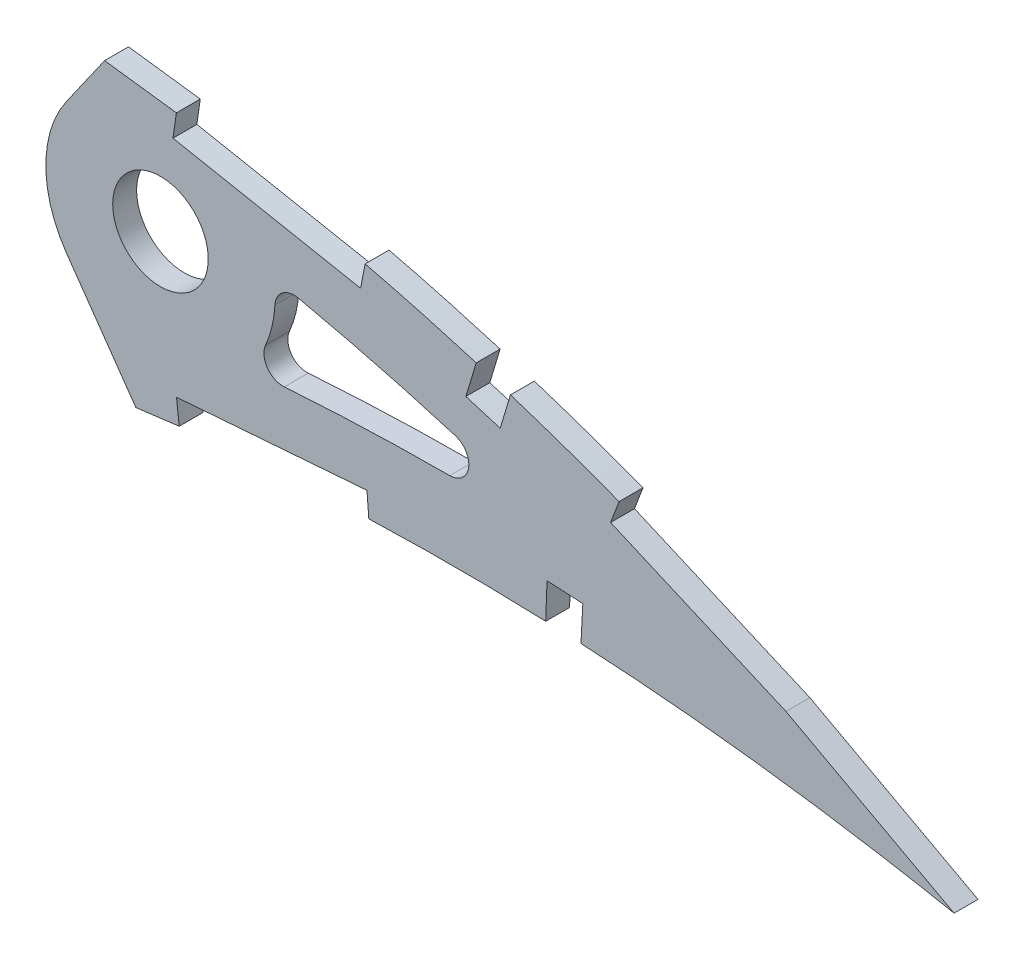
SolidWorks part; units mm, degrees
ref_plane "Front Plane" through (0, 0, 0) normal (0, 0, 1) x (1, 0, 0)
ref_plane "Top Plane" through (0, 0, 0) normal (0, 1, 0) x (1, 0, 0)
ref_plane "Right Plane" through (0, 0, 0) normal (1, 0, 0) x (0, 0, -1)
curve "Curve1"
  spline degree 3 poles (383.949, 0.5986, 0) (383.9196, 0.6168, 0) (383.802, 0.6894, 0) (383.5372, 0.8518, 0) (383.0962, 1.1224, 0) (382.4788, 1.4992, 0) (381.6856, 1.9812, 0) (380.716, 2.5651, 0) (379.5708, 3.249, 0) (378.2502, 4.0295, 0) (376.7543, 4.9032, 0) (375.0838, 5.8664, 0) (373.2387, 6.9137, 0) (371.2197, 8.0407, 0) (369.0276, 9.2423, 0) (366.6628, 10.5128, 0) (364.1261, 11.8459, 0) (361.4185, 13.2358, 0) (358.5405, 14.6749, 0) (355.4934, 16.1571, 0) (352.2782, 17.675, 0) (348.8962, 19.2207, 0) (345.3491, 20.7877, 0) (341.638, 22.3663, 0) (337.765, 23.9497, 0) (333.7318, 25.5289, 0) (329.5407, 27.0966, 0) (325.1933, 28.6428, 0) (320.6929, 30.1607, 0) (316.0417, 31.6403, 0) (311.2431, 33.0737, 0) (306.2997, 34.4516, 0) (301.2157, 35.767, 0) (295.9944, 37.0101, 0) (290.6401, 38.1728, 0) (285.1572, 39.2479, 0) (279.5502, 40.2249, 0) (273.8346, 41.1028, 0) (268.1025, 41.8331, 0) (262.3821, 42.5494, 0) (256.6703, 43.2222, 0) (250.8886, 43.8666, 0) (245.0428, 44.4788, 0) (239.1384, 45.057, 0) (233.1816, 45.5987, 0) (227.1785, 46.1022, 0) (221.135, 46.5647, 0) (215.0573, 46.9856, 0) (208.9515, 47.361, 0) (202.8242, 47.6908, 0) (196.6815, 47.9725, 0) (190.5298, 48.2044, 0) (184.3757, 48.385, 0) (178.2255, 48.5125, 0) (172.0859, 48.5861, 0) (165.9633, 48.6039, 0) (159.8643, 48.5655, 0) (153.7954, 48.4696, 0) (147.7632, 48.3149, 0) (141.7741, 48.1011, 0) (135.8345, 47.8283, 0) (129.951, 47.4942, 0) (124.1299, 47.1009, 0) (118.3778, 46.6469, 0) (112.701, 46.1319, 0) (107.1053, 45.5581, 0) (101.5971, 44.9239, 0) (96.1822, 44.2312, 0) (90.8666, 43.4813, 0) (85.6562, 42.6738, 0) (80.5566, 41.8111, 0) (75.5733, 40.894, 0) (70.7116, 39.9252, 0) (65.9768, 38.9049, 0) (61.3739, 37.8363, 0) (56.9076, 36.7211, 0) (52.5828, 35.5615, 0) (48.4038, 34.3602, 0) (44.375, 33.1199, 0) (40.5009, 31.842, 0) (36.7845, 30.5314, 0) (33.2304, 29.1889, 0) (29.8413, 27.8188, 0) (26.6212, 26.4228, 0) (23.5724, 25.0052, 0) (20.6984, 23.5677, 0) (18.0014, 22.1143, 0) (15.4839, 20.6472, 0) (13.1483, 19.1691, 0) (10.9958, 17.6837, 0) (9.0293, 16.1921, 0) (7.2493, 14.698, 0) (5.6571, 13.2036, 0) (4.255, 11.71, 0) (3.0428, 10.2198, 0) (2.0222, 8.7343, 0) (1.1933, 7.2547, 0) (0.558, 5.7822, 0) (0.1157, 4.3176, 0) (-0.1263, 2.863, 0) (-0.1866, 1.4174, 0) (-0.0621, 0.4718, 0) (0, 0, 0) knots 0 0 0 0 0.000254 0.001015 0.002283 0.004057 0.006331 0.009105 0.012374 0.016134 0.02038 0.025106 0.030306 0.035972 0.0421 0.048678 0.055702 0.06316 0.071046 0.07935 0.088063 0.097176 0.106678 0.116562 0.126814 0.137428 0.148394 0.1597 0.171338 0.183298 0.19557 0.208144 0.221012 0.234162 0.247587 0.261277 0.275223 0.289414 0.303771 0.317689 0.331784 0.34604 0.360444 0.374983 0.38964 0.404403 0.419257 0.434187 0.449177 0.464215 0.479284 0.49437 0.509458 0.524532 0.539579 0.554583 0.56953 0.584403 0.599191 0.613877 0.628447 0.642889 0.657186 0.671326 0.685294 0.699078 0.712665 0.726043 0.739198 0.752118 0.764792 0.777208 0.789356 0.801224 0.812804 0.824083 0.835055 0.84571 0.856038 0.866034 0.875689 0.884998 0.893953 0.902553 0.910789 0.918661 0.926166 0.933303 0.940071 0.946475 0.952518 0.958205 0.963547 0.968557 0.97325 0.977651 0.981787 0.985694 0.989415 0.993001 0.996508 1 1 1 1
curve "Curve2"
  spline degree 3 poles (0, 0, 0) (0.0986, -0.4654, 0) (0.2962, -1.3985, 0) (0.8332, -2.7416, 0) (1.5434, -4.0328, 0) (2.4415, -5.2686, 0) (3.5218, -6.4485, 0) (4.7818, -7.574, 0) (6.2202, -8.6443, 0) (7.8352, -9.659, 0) (9.6244, -10.6191, 0) (11.5859, -11.5241, 0) (13.7178, -12.3737, 0) (16.0178, -13.1667, 0) (18.4831, -13.9043, 0) (21.1113, -14.5848, 0) (23.8995, -15.2091, 0) (26.845, -15.7756, 0) (29.9446, -16.2848, 0) (33.195, -16.7366, 0) (36.593, -17.1311, 0) (40.1351, -17.4676, 0) (43.8179, -17.7467, 0) (47.6377, -17.9687, 0) (51.5909, -18.1343, 0) (55.6735, -18.2428, 0) (59.8817, -18.2959, 0) (64.2115, -18.2945, 0) (68.6589, -18.238, 0) (73.2199, -18.1297, 0) (77.8902, -17.9689, 0) (82.6657, -17.7575, 0) (87.5419, -17.4976, 0) (92.5144, -17.1902, 0) (97.5791, -16.8365, 0) (102.7313, -16.4394, 0) (107.9665, -16, 0) (113.2801, -15.5207, 0) (118.6674, -15.0039, 0) (124.1237, -14.4514, 0) (129.6442, -13.8657, 0) (135.2241, -13.2487, 0) (140.8584, -12.6036, 0) (146.5422, -11.9317, 0) (152.2705, -11.2369, 0) (158.0381, -10.5203, 0) (163.84, -9.7848, 0) (169.6711, -9.0339, 0) (175.5259, -8.2674, 0) (181.3995, -7.4908, 0) (187.2862, -6.7036, 0) (193.1809, -5.9096, 0) (199.0781, -5.1115, 0) (204.9721, -4.3094, 0) (210.8578, -3.5066, 0) (216.7295, -2.7054, 0) (222.5817, -1.9059, 0) (228.409, -1.112, 0) (234.2055, -0.3236, 0) (239.9659, 0.4577, 0) (245.6847, 1.2295, 0) (251.3565, 1.9909, 0) (256.9754, 2.7413, 0) (262.5357, 3.4812, 0) (267.9487, 4.188, 0) (273.2002, 4.8993, 0) (278.3079, 5.4825, 0) (283.3519, 5.9802, 0) (288.3377, 6.3883, 0) (293.259, 6.7125, 0) (298.1104, 6.9553, 0) (302.886, 7.1201, 0) (307.5799, 7.2116, 0) (312.186, 7.2323, 0) (316.6983, 7.1886, 0) (321.1107, 7.0842, 0) (325.4171, 6.9238, 0) (329.6115, 6.7126, 0) (333.688, 6.4566, 0) (337.6405, 6.1594, 0) (341.4634, 5.828, 0) (345.1508, 5.4673, 0) (348.6971, 5.0813, 0) (352.0971, 4.6782, 0) (355.3453, 4.2606, 0) (358.4369, 3.8354, 0) (361.3669, 3.4069, 0) (364.1307, 2.9806, 0) (366.7239, 2.5605, 0) (369.1422, 2.1521, 0) (371.3821, 1.7594, 0) (373.4394, 1.3862, 0) (375.3115, 1.0371, 0) (376.9946, 0.7139, 0) (378.4864, 0.4219, 0) (379.7842, 0.1625, 0) (380.886, -0.0608, 0) (381.79, -0.247, 0) (382.4947, -0.3932, 0) (382.9989, -0.4995, 0) (383.3019, -0.5627, 0) (383.4365, -0.5914, 0) (383.4701, -0.5986, 0) knots 0 0 0 0 0.003638 0.007293 0.011028 0.014901 0.018963 0.023258 0.027821 0.032679 0.037853 0.043362 0.049215 0.055422 0.061989 0.068918 0.076211 0.083868 0.091887 0.100266 0.109 0.118085 0.127515 0.137285 0.147388 0.157816 0.168563 0.179619 0.190977 0.202627 0.21456 0.226767 0.239236 0.251959 0.264924 0.27812 0.291536 0.30516 0.318981 0.332985 0.347163 0.361499 0.375981 0.390597 0.405333 0.420175 0.43511 0.450124 0.465203 0.480333 0.495501 0.51069 0.525887 0.541078 0.556247 0.571382 0.586466 0.601485 0.616424 0.631269 0.646007 0.660621 0.675098 0.689423 0.703582 0.716908 0.730009 0.742952 0.755726 0.76832 0.780724 0.792927 0.804916 0.816679 0.828204 0.839475 0.850481 0.861208 0.871639 0.881763 0.891564 0.901027 0.910139 0.918884 0.927249 0.935221 0.942785 0.949928 0.956638 0.962904 0.968712 0.974054 0.978918 0.983297 0.98718 0.990561 0.993433 0.995791 0.99763 0.998946 0.999737 1 1 1 1
sketch "Sketch1" plane through (0, 0, 0) normal (0, 0, 1) x (1, 0, 0)
  line L23 (383.4597, -0.5986) -> (387.1511, -1.386)
  line L24 (383.9386, 0.5986) -> (387.1511, -1.386)
  spline S4 degree 3 poles (0, 0) (0.0986, -0.4654) (0.2962, -1.3984) (0.8332, -2.7416) (1.5433, -4.0327) (2.4415, -5.2684) (3.5217, -6.4484) (4.7816, -7.5738) (6.22, -8.6441) (7.835, -9.6587) (9.6242, -10.6188) (11.5856, -11.5238) (13.7174, -12.3733) (16.0173, -13.1663) (18.4826, -13.9039) (21.1108, -14.5844) (23.8989, -15.2087) (26.8443, -15.7751) (29.9438, -16.2844) (33.1941, -16.7361) (36.592, -17.1306) (40.134, -17.4671) (43.8167, -17.7462) (47.6365, -17.9682) (51.5895, -18.1338) (55.672, -18.2423) (59.88, -18.2954) (64.2098, -18.294) (68.657, -18.2375) (73.2179, -18.1293) (77.8881, -17.9684) (82.6634, -17.757) (87.5395, -17.4972) (92.5119, -17.1897) (97.5764, -16.836) (102.7286, -16.439) (107.9636, -15.9995) (113.2771, -15.5202) (118.6642, -15.0035) (124.1204, -14.451) (129.6407, -13.8653) (135.2204, -13.2483) (140.8546, -12.6033) (146.5382, -11.9314) (152.2664, -11.2365) (158.0338, -10.52) (163.8356, -9.7845) (169.6665, -9.0336) (175.5212, -8.2672) (181.3946, -7.4906) (187.2811, -6.7034) (193.1757, -5.9095) (199.0727, -5.1113) (204.9666, -4.3092) (210.8521, -3.5065) (216.7237, -2.7054) (222.5757, -1.9059) (228.4028, -1.112) (234.1992, -0.3236) (239.9594, 0.4576) (245.6781, 1.2294) (251.3497, 1.9908) (256.9684, 2.7413) (262.5286, 3.4811) (267.9415, 4.1879) (273.1928, 4.8992) (278.3003, 5.4823) (283.3443, 5.98) (288.3299, 6.3881) (293.2511, 6.7123) (298.1023, 6.9552) (302.8778, 7.1199) (307.5715, 7.2114) (312.1776, 7.2321) (316.6897, 7.1884) (321.102, 7.084) (325.4083, 6.9236) (329.6026, 6.7124) (333.679, 6.4564) (337.6313, 6.1592) (341.4541, 5.8278) (345.1414, 5.4671) (348.6876, 5.0812) (352.0875, 4.6781) (355.3357, 4.2605) (358.4272, 3.8353) (361.3571, 3.4068) (364.1208, 2.9805) (366.7139, 2.5604) (369.1322, 2.1521) (371.372, 1.7594) (373.4293, 1.3862) (375.3013, 1.0371) (376.9844, 0.7139) (378.4761, 0.4219) (379.7739, 0.1625) (380.8757, -0.0608) (381.7796, -0.247) (382.4844, -0.3932) (382.9885, -0.4994) (383.2915, -0.5627) (383.4261, -0.5914) (383.4597, -0.5986) knots 0 0 0 0 0.003638 0.007293 0.011028 0.014901 0.018963 0.023258 0.027821 0.032679 0.037853 0.043362 0.049215 0.055422 0.061989 0.068918 0.076211 0.083868 0.091887 0.100266 0.109 0.118085 0.127515 0.137285 0.147388 0.157816 0.168563 0.179619 0.190977 0.202627 0.21456 0.226767 0.239236 0.251959 0.264924 0.27812 0.291536 0.30516 0.318981 0.332985 0.347163 0.361499 0.375981 0.390597 0.405333 0.420175 0.43511 0.450124 0.465203 0.480333 0.495501 0.51069 0.525887 0.541078 0.556247 0.571382 0.586466 0.601485 0.616424 0.631269 0.646007 0.660621 0.675098 0.689423 0.703582 0.716908 0.730009 0.742952 0.755726 0.76832 0.780724 0.792927 0.804916 0.816679 0.828204 0.839475 0.850481 0.861208 0.871639 0.881763 0.891564 0.901027 0.910139 0.918884 0.927249 0.935221 0.942785 0.949928 0.956638 0.962904 0.968712 0.974054 0.978918 0.983297 0.98718 0.990561 0.993433 0.995791 0.99763 0.998946 0.999737 1 1 1 1
  spline S5 degree 3 poles (383.9386, 0.5986) (383.9092, 0.6167) (383.7916, 0.6893) (383.5268, 0.8518) (383.0858, 1.1223) (382.4685, 1.4991) (381.6752, 1.9811) (380.7057, 2.565) (379.5606, 3.2489) (378.24, 4.0294) (376.7441, 4.9031) (375.0736, 5.8662) (373.2286, 6.9135) (371.2097, 8.0405) (369.0176, 9.242) (366.6529, 10.5125) (364.1162, 11.8456) (361.4087, 13.2354) (358.5307, 14.6745) (355.4837, 16.1566) (352.2687, 17.6745) (348.8867, 19.2201) (345.3398, 20.7871) (341.6288, 22.3657) (337.7559, 23.949) (333.7228, 25.5282) (329.5317, 27.0959) (325.1845, 28.642) (320.6843, 30.1598) (316.0332, 31.6395) (311.2346, 33.0728) (306.2914, 34.4507) (301.2076, 35.766) (295.9864, 37.0091) (290.6322, 38.1717) (285.1495, 39.2469) (279.5426, 40.2238) (273.8272, 41.1017) (268.0952, 41.832) (262.375, 42.5482) (256.6633, 43.2211) (250.8818, 43.8654) (245.0361, 44.4776) (239.1319, 45.0558) (233.1753, 45.5974) (227.1724, 46.1009) (221.129, 46.5635) (215.0515, 46.9843) (208.9459, 47.3597) (202.8187, 47.6895) (196.6762, 47.9712) (190.5246, 48.2031) (184.3707, 48.3836) (178.2206, 48.5111) (172.0812, 48.5848) (165.9588, 48.6026) (159.86, 48.5642) (153.7912, 48.4683) (147.7592, 48.3136) (141.7702, 48.0998) (135.8308, 47.827) (129.9475, 47.4929) (124.1266, 47.0997) (118.3746, 46.6456) (112.6979, 46.1306) (107.1024, 45.5568) (101.5944, 44.9227) (96.1796, 44.23) (90.8641, 43.4801) (85.6539, 42.6727) (80.5544, 41.81) (75.5713, 40.8929) (70.7097, 39.9241) (65.975, 38.9039) (61.3722, 37.8353) (56.906, 36.7201) (52.5814, 35.5606) (48.4025, 34.3593) (44.3738, 33.119) (40.4998, 31.8412) (36.7835, 30.5306) (33.2295, 29.1881) (29.8405, 27.818) (26.6204, 26.4221) (23.5718, 25.0045) (20.6979, 23.5671) (18.0009, 22.1137) (15.4834, 20.6466) (13.148, 19.1685) (10.9955, 17.6833) (9.029, 16.1917) (7.2491, 14.6976) (5.657, 13.2033) (4.2548, 11.7097) (3.0427, 10.2196) (2.0221, 8.734) (1.1932, 7.2545) (0.558, 5.782) (0.1157, 4.3174) (-0.1263, 2.8629) (-0.1866, 1.4173) (-0.0621, 0.4717) (0, 0) knots 0 0 0 0 0.000254 0.001015 0.002283 0.004057 0.006331 0.009105 0.012374 0.016134 0.02038 0.025106 0.030306 0.035972 0.0421 0.048678 0.055702 0.06316 0.071046 0.07935 0.088063 0.097176 0.106678 0.116562 0.126814 0.137428 0.148394 0.1597 0.171338 0.183298 0.19557 0.208144 0.221012 0.234162 0.247587 0.261277 0.275223 0.289414 0.303771 0.317689 0.331784 0.34604 0.360444 0.374983 0.38964 0.404403 0.419257 0.434187 0.449177 0.464215 0.479284 0.49437 0.509458 0.524532 0.539579 0.554583 0.56953 0.584403 0.599191 0.613877 0.628447 0.642889 0.657186 0.671326 0.685294 0.699078 0.712665 0.726043 0.739198 0.752118 0.764792 0.777208 0.789356 0.801224 0.812804 0.824083 0.835055 0.84571 0.856038 0.866034 0.875689 0.884998 0.893953 0.902553 0.910789 0.918661 0.926166 0.933303 0.940071 0.946475 0.952518 0.958205 0.963547 0.968557 0.97325 0.977651 0.981787 0.985694 0.989415 0.993001 0.996508 1 1 1 1
extrude "Boss-Extrude1" add sketch "Sketch1" along normal blind 3.175
sketch "Sketch3" plane through (0, 0, 0) normal (0, 0, -1) x (-1, 0, 0)
  circle A1 centre (-272.4199, 26.2554) radius 6.35
extrude "Cut-Extrude2" cut sketch "Sketch3" against normal blind 7.62
sketch "Sketch4" plane through (0, 0, 3.175) normal (0, 0, 1) x (1, 0, 0)
  line L0 (272.4199, 26.2554) -> (275.6183, 26.2554)
  line L1 (259.936, 34.9967) -> (264.9932, 42.2191)
  line L2 (259.936, 17.5141) -> (269.1511, 4.3535)
  circle A0 centre (272.4199, 26.2554) radius 6.35 construction
  circle A1 centre (272.4199, 26.2554) radius 6.35
  circle A2 centre (272.4199, 26.2554) radius 15.24
  spline S0 degree 3 poles (-2900.5811, -762.1564) (60.7171, 58.1372) (-7.1311, 17.1797) (0.8332, -2.7416) (1.5433, -4.0327) (2.4415, -5.2684) (3.5217, -6.4484) (4.7816, -7.5738) (6.22, -8.6441) (7.835, -9.6587) (9.6242, -10.6188) (11.5856, -11.5238) (13.7174, -12.3733) (16.0173, -13.1663) (18.4826, -13.9039) (21.1108, -14.5844) (23.8989, -15.2087) (26.8443, -15.7751) (29.9438, -16.2844) (33.1941, -16.7361) (36.592, -17.1306) (40.134, -17.4671) (43.8167, -17.7462) (47.6365, -17.9682) (51.5895, -18.1338) (55.672, -18.2423) (59.88, -18.2954) (64.2098, -18.294) (68.657, -18.2375) (73.2179, -18.1293) (77.8881, -17.9684) (82.6634, -17.757) (87.5395, -17.4972) (92.5119, -17.1897) (97.5764, -16.836) (102.7286, -16.439) (107.9636, -15.9995) (113.2771, -15.5202) (118.6642, -15.0035) (124.1204, -14.451) (129.6407, -13.8653) (135.2204, -13.2483) (140.8546, -12.6033) (146.5382, -11.9314) (152.2664, -11.2365) (158.0338, -10.52) (163.8356, -9.7845) (169.6665, -9.0336) (175.5212, -8.2672) (181.3946, -7.4906) (187.2811, -6.7034) (193.1757, -5.9095) (199.0727, -5.1113) (204.9666, -4.3092) (210.8521, -3.5065) (216.7237, -2.7054) (222.5757, -1.9059) (228.4028, -1.112) (234.1992, -0.3236) (239.9594, 0.4576) (245.6781, 1.2294) (251.3497, 1.9908) (256.9684, 2.7413) (262.5286, 3.4811) (267.9415, 4.1879) (273.1928, 4.8992) (278.3003, 5.4823) (283.3443, 5.98) (288.3299, 6.3881) (293.2511, 6.7123) (298.1023, 6.9552) (302.8778, 7.1199) (307.5715, 7.2114) (312.1776, 7.2321) (316.6897, 7.1884) (321.102, 7.084) (325.4083, 6.9236) (329.6026, 6.7124) (333.679, 6.4564) (337.6313, 6.1592) (341.4541, 5.8278) (345.1414, 5.4671) (348.6876, 5.0812) (352.0875, 4.6781) (355.3357, 4.2605) (358.4272, 3.8353) (361.3571, 3.4068) (364.1208, 2.9805) (366.7139, 2.5604) (369.1322, 2.1521) (371.372, 1.7594) (373.4293, 1.3862) (375.3013, 1.0371) (376.9844, 0.7139) (378.4761, 0.4219) (379.7739, 0.1625) (380.8757, -0.0608) (381.7796, -0.247) (382.4844, -0.3932) (382.9885, -0.4994) (397.7614, -3.5828) (410.8952, -13.5854) (1047.3532, 2924.2375) knots -0.152541 -0.152541 -0.152541 -0.152541 0.003638 0.007293 0.011028 0.014901 0.018963 0.023258 0.027821 0.032679 0.037853 0.043362 0.049215 0.055422 0.061989 0.068918 0.076211 0.083868 0.091887 0.100266 0.109 0.118085 0.127515 0.137285 0.147388 0.157816 0.168563 0.179619 0.190977 0.202627 0.21456 0.226767 0.239236 0.251959 0.264924 0.27812 0.291536 0.30516 0.318981 0.332985 0.347163 0.361499 0.375981 0.390597 0.405333 0.420175 0.43511 0.450124 0.465203 0.480333 0.495501 0.51069 0.525887 0.541078 0.556247 0.571382 0.586466 0.601485 0.616424 0.631269 0.646007 0.660621 0.675098 0.689423 0.703582 0.716908 0.730009 0.742952 0.755726 0.76832 0.780724 0.792927 0.804916 0.816679 0.828204 0.839475 0.850481 0.861208 0.871639 0.881763 0.891564 0.901027 0.910139 0.918884 0.927249 0.935221 0.942785 0.949928 0.956638 0.962904 0.968712 0.974054 0.978918 0.983297 0.98718 0.990561 0.993433 0.995791 0.99763 0.998946 0.999737 1.113214 1.113214 1.113214 1.113214 only from (0, 0) to (383.4597, -0.5986) construction
  spline S1 degree 3 poles (1998.8466, 2527.3991) (408.7537, -22.1004) (397.8856, -7.9557) (383.5268, 0.8518) (383.0858, 1.1223) (382.4685, 1.4991) (381.6752, 1.9811) (380.7057, 2.565) (379.5606, 3.2489) (378.24, 4.0294) (376.7441, 4.9031) (375.0736, 5.8662) (373.2286, 6.9135) (371.2097, 8.0405) (369.0176, 9.242) (366.6529, 10.5125) (364.1162, 11.8456) (361.4087, 13.2354) (358.5307, 14.6745) (355.4837, 16.1566) (352.2687, 17.6745) (348.8867, 19.2201) (345.3398, 20.7871) (341.6288, 22.3657) (337.7559, 23.949) (333.7228, 25.5282) (329.5317, 27.0959) (325.1845, 28.642) (320.6843, 30.1598) (316.0332, 31.6395) (311.2346, 33.0728) (306.2914, 34.4507) (301.2076, 35.766) (295.9864, 37.0091) (290.6322, 38.1717) (285.1495, 39.2469) (279.5426, 40.2238) (273.8272, 41.1017) (268.0952, 41.832) (262.375, 42.5482) (256.6633, 43.2211) (250.8818, 43.8654) (245.0361, 44.4776) (239.1319, 45.0558) (233.1753, 45.5974) (227.1724, 46.1009) (221.129, 46.5635) (215.0515, 46.9843) (208.9459, 47.3597) (202.8187, 47.6895) (196.6762, 47.9712) (190.5246, 48.2031) (184.3707, 48.3836) (178.2206, 48.5111) (172.0812, 48.5848) (165.9588, 48.6026) (159.86, 48.5642) (153.7912, 48.4683) (147.7592, 48.3136) (141.7702, 48.0998) (135.8308, 47.827) (129.9475, 47.4929) (124.1266, 47.0997) (118.3746, 46.6456) (112.6979, 46.1306) (107.1024, 45.5568) (101.5944, 44.9227) (96.1796, 44.23) (90.8641, 43.4801) (85.6539, 42.6727) (80.5544, 41.81) (75.5713, 40.8929) (70.7097, 39.9241) (65.975, 38.9039) (61.3722, 37.8353) (56.906, 36.7201) (52.5814, 35.5606) (48.4025, 34.3593) (44.3738, 33.119) (40.4998, 31.8412) (36.7835, 30.5306) (33.2295, 29.1881) (29.8405, 27.818) (26.6204, 26.4221) (23.5718, 25.0045) (20.6979, 23.5671) (18.0009, 22.1137) (15.4834, 20.6466) (13.148, 19.1685) (10.9955, 17.6833) (9.029, 16.1917) (7.2491, 14.6976) (5.657, 13.2033) (4.2548, 11.7097) (3.0427, 10.2196) (2.0221, 8.734) (1.1932, 7.2545) (0.558, 5.782) (0.1157, 4.3174) (-0.1263, 2.8629) (-1.0184, -18.5368) (76.7539, -34.5403) (-2989.0976, -246.1964) knots -0.121519 -0.121519 -0.121519 -0.121519 0.000254 0.001015 0.002283 0.004057 0.006331 0.009105 0.012374 0.016134 0.02038 0.025106 0.030306 0.035972 0.0421 0.048678 0.055702 0.06316 0.071046 0.07935 0.088063 0.097176 0.106678 0.116562 0.126814 0.137428 0.148394 0.1597 0.171338 0.183298 0.19557 0.208144 0.221012 0.234162 0.247587 0.261277 0.275223 0.289414 0.303771 0.317689 0.331784 0.34604 0.360444 0.374983 0.38964 0.404403 0.419257 0.434187 0.449177 0.464215 0.479284 0.49437 0.509458 0.524532 0.539579 0.554583 0.56953 0.584403 0.599191 0.613877 0.628447 0.642889 0.657186 0.671326 0.685294 0.699078 0.712665 0.726043 0.739198 0.752118 0.764792 0.777208 0.789356 0.801224 0.812804 0.824083 0.835055 0.84571 0.856038 0.866034 0.875689 0.884998 0.893953 0.902553 0.910789 0.918661 0.926166 0.933303 0.940071 0.946475 0.952518 0.958205 0.963547 0.968557 0.97325 0.977651 0.981787 0.985694 0.989415 0.993001 0.996508 1.146107 1.146107 1.146107 1.146107 only from (383.9386, 0.5986) to (0, 0) construction
  spline S2 degree 3 poles (161.4571, -10.0855) (162.2464, -9.9853) (164.9804, -9.6371) (169.6665, -9.0336) (175.5212, -8.2672) (181.3946, -7.4906) (187.2811, -6.7034) (193.1757, -5.9095) (199.0727, -5.1113) (204.9666, -4.3092) (210.8521, -3.5065) (216.7237, -2.7054) (222.5757, -1.9059) (228.4028, -1.112) (234.1992, -0.3236) (239.9594, 0.4576) (245.6781, 1.2294) (251.3497, 1.9908) (256.9684, 2.7413) (262.5286, 3.4811) (267.9415, 4.1879) (273.1928, 4.8992) (278.3003, 5.4823) (283.3443, 5.98) (288.3299, 6.3881) (293.2511, 6.7123) (298.1023, 6.9552) (302.8778, 7.1199) (307.5715, 7.2114) (312.1776, 7.2321) (316.6897, 7.1884) (321.102, 7.084) (325.4083, 6.9236) (329.6026, 6.7124) (333.679, 6.4564) (337.6313, 6.1592) (341.4541, 5.8278) (345.1414, 5.4671) (348.6876, 5.0812) (352.0875, 4.6781) (355.3357, 4.2605) (358.4272, 3.8353) (361.3571, 3.4068) (364.1208, 2.9805) (366.7139, 2.5604) (369.1322, 2.1521) (371.372, 1.7594) (373.4293, 1.3862) (375.3013, 1.0371) (376.9844, 0.7139) (378.4761, 0.4219) (379.7739, 0.1625) (380.8757, -0.0608) (381.7796, -0.247) (382.4844, -0.3932) (382.9885, -0.4994) (383.2915, -0.5627) (383.4261, -0.5914) (383.4597, -0.5986) knots 0.429016 0.429016 0.429016 0.429016 0.43511 0.450124 0.465203 0.480333 0.495501 0.51069 0.525887 0.541078 0.556247 0.571382 0.586466 0.601485 0.616424 0.631269 0.646007 0.660621 0.675098 0.689423 0.703582 0.716908 0.730009 0.742952 0.755726 0.76832 0.780724 0.792927 0.804916 0.816679 0.828204 0.839475 0.850481 0.861208 0.871639 0.881763 0.891564 0.901027 0.910139 0.918884 0.927249 0.935221 0.942785 0.949928 0.956638 0.962904 0.968712 0.974054 0.978918 0.983297 0.98718 0.990561 0.993433 0.995791 0.99763 0.998946 0.999737 1 1 1 1
  spline S3 degree 3 poles (383.9386, 0.5986) (383.9092, 0.6167) (383.7916, 0.6893) (383.5268, 0.8518) (383.0858, 1.1223) (382.4685, 1.4991) (381.6752, 1.9811) (380.7057, 2.565) (379.5606, 3.2489) (378.24, 4.0294) (376.7441, 4.9031) (375.0736, 5.8662) (373.2286, 6.9135) (371.2097, 8.0405) (369.0176, 9.242) (366.6529, 10.5125) (364.1162, 11.8456) (361.4087, 13.2354) (358.5307, 14.6745) (355.4837, 16.1566) (352.2687, 17.6745) (348.8867, 19.2201) (345.3398, 20.7871) (341.6288, 22.3657) (337.7559, 23.949) (333.7228, 25.5282) (329.5317, 27.0959) (325.1845, 28.642) (320.6843, 30.1598) (316.0332, 31.6395) (311.2346, 33.0728) (306.2914, 34.4507) (301.2076, 35.766) (295.9864, 37.0091) (290.6322, 38.1717) (285.1495, 39.2469) (279.5426, 40.2238) (273.8272, 41.1017) (268.0952, 41.832) (262.375, 42.5482) (256.6633, 43.2211) (250.8818, 43.8654) (245.0361, 44.4776) (239.1319, 45.0558) (233.1753, 45.5974) (227.1724, 46.1009) (221.129, 46.5635) (215.0515, 46.9843) (208.9459, 47.3597) (202.8187, 47.6895) (196.6762, 47.9712) (190.5246, 48.2031) (184.3707, 48.3836) (178.2206, 48.5111) (172.0812, 48.5848) (165.9588, 48.6026) (159.86, 48.5642) (153.5038, 48.4638) (149.182, 48.3499) (146.8838, 48.276) knots 0 0 0 0 0.000254 0.001015 0.002283 0.004057 0.006331 0.009105 0.012374 0.016134 0.02038 0.025106 0.030306 0.035972 0.0421 0.048678 0.055702 0.06316 0.071046 0.07935 0.088063 0.097176 0.106678 0.116562 0.126814 0.137428 0.148394 0.1597 0.171338 0.183298 0.19557 0.208144 0.221012 0.234162 0.247587 0.261277 0.275223 0.289414 0.303771 0.317689 0.331784 0.34604 0.360444 0.374983 0.38964 0.404403 0.419257 0.434187 0.449177 0.464215 0.479284 0.49437 0.509458 0.524532 0.539579 0.554583 0.56953 0.584403 0.601304 0.601304 0.601304 0.601304
  spline S4 degree 1 poles (378.5989, -8.0451) (147.21, 38.1213) knots 0 0 1 1 construction
  spline S5 degree 3 poles (378.5989, -8.0451) (378.472, -7.9667) (378.2234, -7.8142) (377.6805, -7.4812) (376.7611, -6.9205) (374.9109, -5.8032) (371.1788, -3.5966) (363.6516, 0.6712) (348.2892, 8.639) (330.0962, 16.359) (311.3792, 22.5636) (297.107, 26.4342) (285.0856, 28.9814) (276.5539, 30.4164) (271.7323, 31.12) (268.0333, 31.5987) (264.2273, 32.0776) (259.2208, 32.6948) (250.4292, 33.7129) (237.8617, 35.009) (222.7587, 36.2937) (202.6061, 37.6338) (177.3909, 38.5745) (157.2697, 38.4445) (147.21, 38.1213) knots 0 0 0 0 0.001174 0.002349 0.004698 0.009395 0.018791 0.037581 0.075163 0.150326 0.187907 0.225489 0.26307 0.281861 0.291256 0.300652 0.310047 0.319443 0.338233 0.375815 0.413396 0.450978 0.526141 0.601304 0.601304 0.601304 0.601304
  spline S6 degree 1 poles (160.178, -0.0063) (385.5793, 9.3379) knots 0 0 1 1 construction
  spline S7 degree 3 poles (160.178, -0.0063) (169.3975, 1.1637) (187.8091, 3.6001) (210.885, 6.7523) (229.3545, 9.2731) (243.2292, 11.1537) (254.7583, 12.7013) (262.905, 13.7751) (267.4672, 14.3775) (270.981, 14.8497) (274.6098, 15.2908) (279.3773, 15.8089) (285.3756, 16.3645) (292.5728, 16.8641) (302.1885, 17.3159) (314.2133, 17.4755) (333.4344, 16.8874) (352.5648, 15.0706) (369.1185, 12.5101) (377.3698, 10.9967) (381.4564, 10.1902) (383.3728, 9.7984) (384.2388, 9.6192) (384.6955, 9.524) (385.0455, 9.4502) (385.329, 9.391) (385.4982, 9.3552) (385.5793, 9.3379) knots 0.429016 0.429016 0.429016 0.429016 0.500389 0.571762 0.607448 0.643135 0.678821 0.696665 0.705586 0.714508 0.723429 0.732351 0.750194 0.768038 0.785881 0.821567 0.857254 0.928627 0.964313 0.982157 0.991078 0.995539 0.996654 0.99777 0.998885 0.999442 1 1 1 1
  dimension "D1" = 30.48
  dimension "D2" = 55
  dimension "D3" = 55
  dimension "D4" = 10.16
extrude "Cut-Extrude3" cut sketch "Sketch4" against normal through all
sketch "Sketch5" plane through (0, 0, 3.175) normal (0, 0, 1) x (1, 0, 0)
  line L0 (274.5345, 40.976) -> (274.083, 37.8333)
  line L1 (274.083, 37.8333) -> (299.0226, 33.019)
  line L2 (299.0226, 33.019) -> (299.6244, 36.1364)
  line L3 (274.9174, 5.0903) -> (274.5453, 8.2434)
  line L4 (274.5453, 8.2434) -> (299.8708, 10.1869)
  line L5 (299.8708, 10.1869) -> (300.1138, 7.0212)
  line L6 (333.3826, 25.6462) -> (332.2514, 22.6795)
  line L7 (332.2514, 22.6795) -> (355.5602, 12.5869)
  line L8 (355.5602, 12.5869) -> (377.9168, 0.5311)
  line L9 (377.9168, 0.5311) -> (379.5381, 3.2609)
  line L10 (355.5602, 12.5869) -> (356.9478, 15.4426)
  line L11 (314.393, 32.1244) -> (313.0177, 27.5648)
  line L12 (313.0177, 27.5648) -> (317.5773, 26.1895)
  line L13 (317.5773, 26.1895) -> (318.9408, 30.7101)
  line L14 (323.625, 6.9875) -> (323.8072, 11.7465)
  line L15 (323.8072, 11.7465) -> (328.5631, 11.4961)
  line L16 (328.5631, 11.4961) -> (328.3145, 6.7742)
  line L17 (333.3826, 25.6462) -> (318.9408, 30.7101) construction
  line L18 (314.393, 32.1244) -> (299.6244, 36.1364) construction
  line L19 (355.5602, 12.5869) -> (351.7355, 4.7158)
  line L20 (351.7355, 4.7158) -> (328.3145, 6.7742) construction
  line L21 (323.625, 6.9875) -> (300.1138, 7.0212) construction
  circle A0 centre (272.4199, 26.2554) radius 6.35 construction
  circle A1 centre (272.4199, 26.2554) radius 6.35
  spline S0 degree 3 poles (-210.4395, 1941.1642) (121.3297, -52.1941) (196.4933, -3.8575) (278.3003, 5.4823) (283.3443, 5.98) (288.3299, 6.3881) (293.2511, 6.7123) (298.1023, 6.9552) (302.8778, 7.1199) (307.5715, 7.2114) (312.1776, 7.2321) (316.6897, 7.1884) (321.102, 7.084) (325.4083, 6.9236) (329.6026, 6.7124) (333.679, 6.4564) (337.6313, 6.1592) (341.4541, 5.8278) (345.1414, 5.4671) (348.6876, 5.0812) (352.0875, 4.6781) (355.3357, 4.2605) (358.4272, 3.8353) (361.3571, 3.4068) (364.1208, 2.9805) (366.7139, 2.5604) (369.1322, 2.1521) (371.372, 1.7594) (373.4293, 1.3862) (375.3013, 1.0371) (376.9844, 0.7139) (378.4761, 0.4219) (379.7739, 0.1625) (380.8757, -0.0608) (381.7796, -0.247) (382.4844, -0.3932) (382.9885, -0.4994) (395.9321, -3.201) (407.582, -11.1888) (835.0263, 1947.3652) knots 0.11236 0.11236 0.11236 0.11236 0.716908 0.730009 0.742952 0.755726 0.76832 0.780724 0.792927 0.804916 0.816679 0.828204 0.839475 0.850481 0.861208 0.871639 0.881763 0.891564 0.901027 0.910139 0.918884 0.927249 0.935221 0.942785 0.949928 0.956638 0.962904 0.968712 0.974054 0.978918 0.983297 0.98718 0.990561 0.993433 0.995791 0.99763 0.998946 0.999737 1.098901 1.098901 1.098901 1.098901 only from (269.1511, 4.3535) to (383.4597, -0.5986) construction
  spline S1 degree 3 poles (1469.2762, 1679.7392) (405.976, -18.6391) (396.1038, -6.8628) (383.5268, 0.8518) (383.0858, 1.1223) (382.4685, 1.4991) (381.6752, 1.9811) (380.7057, 2.565) (379.5606, 3.2489) (378.24, 4.0294) (376.7441, 4.9031) (375.0736, 5.8662) (373.2286, 6.9135) (371.2097, 8.0405) (369.0176, 9.242) (366.6529, 10.5125) (364.1162, 11.8456) (361.4087, 13.2354) (358.5307, 14.6745) (355.4837, 16.1566) (352.2687, 17.6745) (348.8867, 19.2201) (345.3398, 20.7871) (341.6288, 22.3657) (337.7559, 23.949) (333.7228, 25.5282) (329.5317, 27.0959) (325.1845, 28.642) (320.6843, 30.1598) (316.0332, 31.6395) (311.2346, 33.0728) (306.2914, 34.4507) (301.2076, 35.766) (295.9864, 37.0091) (290.6322, 38.1717) (285.1495, 39.2469) (279.5426, 40.2238) (273.8272, 41.1017) (132.45, 59.114) (-8.1155, 65.8482) (-401.8712, -1828.0204) knots -0.106157 -0.106157 -0.106157 -0.106157 0.000254 0.001015 0.002283 0.004057 0.006331 0.009105 0.012374 0.016134 0.02038 0.025106 0.030306 0.035972 0.0421 0.048678 0.055702 0.06316 0.071046 0.07935 0.088063 0.097176 0.106678 0.116562 0.126814 0.137428 0.148394 0.1597 0.171338 0.183298 0.19557 0.208144 0.221012 0.234162 0.247587 0.261277 0.275223 0.289414 0.303771 1.322643 1.322643 1.322643 1.322643 only from (383.9386, 0.5986) to (264.9932, 42.2191) construction
  spline S2 degree 3 poles (269.1511, 4.3535) (270.5083, 4.5347) (273.5611, 4.9412) (278.3003, 5.4823) (283.3443, 5.98) (288.3299, 6.3881) (293.2511, 6.7123) (298.1023, 6.9552) (302.8778, 7.1199) (307.5715, 7.2114) (312.1776, 7.2321) (316.6897, 7.1884) (321.102, 7.084) (325.4083, 6.9236) (329.6026, 6.7124) (333.679, 6.4564) (337.6313, 6.1592) (341.4541, 5.8278) (345.1414, 5.4671) (348.6876, 5.0812) (352.0875, 4.6781) (355.3357, 4.2605) (358.4272, 3.8353) (361.3571, 3.4068) (364.1208, 2.9805) (366.7139, 2.5604) (369.1322, 2.1521) (371.372, 1.7594) (373.4293, 1.3862) (375.3013, 1.0371) (376.9844, 0.7139) (378.4761, 0.4219) (379.7739, 0.1625) (380.8757, -0.0608) (381.7796, -0.247) (382.4844, -0.3932) (382.9885, -0.4994) (383.2915, -0.5627) (383.4261, -0.5914) (383.4597, -0.5986) knots 0.706421 0.706421 0.706421 0.706421 0.716908 0.730009 0.742952 0.755726 0.76832 0.780724 0.792927 0.804916 0.816679 0.828204 0.839475 0.850481 0.861208 0.871639 0.881763 0.891564 0.901027 0.910139 0.918884 0.927249 0.935221 0.942785 0.949928 0.956638 0.962904 0.968712 0.974054 0.978918 0.983297 0.98718 0.990561 0.993433 0.995791 0.99763 0.998946 0.999737 1 1 1 1
  spline S3 degree 3 poles (383.9386, 0.5986) (383.9092, 0.6167) (383.7916, 0.6893) (383.5268, 0.8518) (383.0858, 1.1223) (382.4685, 1.4991) (381.6752, 1.9811) (380.7057, 2.565) (379.5606, 3.2489) (378.24, 4.0294) (376.7441, 4.9031) (375.0736, 5.8662) (373.2286, 6.9135) (371.2097, 8.0405) (369.0176, 9.242) (366.6529, 10.5125) (364.1162, 11.8456) (361.4087, 13.2354) (358.5307, 14.6745) (355.4837, 16.1566) (352.2687, 17.6745) (348.8867, 19.2201) (345.3398, 20.7871) (341.6288, 22.3657) (337.7559, 23.949) (333.7228, 25.5282) (329.5317, 27.0959) (325.1845, 28.642) (320.6843, 30.1598) (316.0332, 31.6395) (311.2346, 33.0728) (306.2914, 34.4507) (301.2076, 35.766) (295.9864, 37.0091) (290.6322, 38.1717) (285.1495, 39.2469) (279.5426, 40.2238) (273.8272, 41.1017) (268.9598, 41.7218) (266.0075, 42.093) (264.9932, 42.2191) knots 0 0 0 0 0.000254 0.001015 0.002283 0.004057 0.006331 0.009105 0.012374 0.016134 0.02038 0.025106 0.030306 0.035972 0.0421 0.048678 0.055702 0.06316 0.071046 0.07935 0.088063 0.097176 0.106678 0.116562 0.126814 0.137428 0.148394 0.1597 0.171338 0.183298 0.19557 0.208144 0.221012 0.234162 0.247587 0.261277 0.275223 0.289414 0.303771 0.311283 0.311283 0.311283 0.311283
  spline M31 degree 3 poles (0, 0) (0.0986, -0.4654) (0.2962, -1.3984) (0.8332, -2.7416) (1.5433, -4.0327) (2.4415, -5.2684) (3.5217, -6.4484) (4.7816, -7.5738) (6.22, -8.6441) (7.835, -9.6587) (9.6242, -10.6188) (11.5856, -11.5238) (13.7174, -12.3733) (16.0173, -13.1663) (18.4826, -13.9039) (21.1108, -14.5844) (23.8989, -15.2087) (26.8443, -15.7751) (29.9438, -16.2844) (33.1941, -16.7361) (36.592, -17.1306) (40.134, -17.4671) (43.8167, -17.7462) (47.6365, -17.9682) (51.5895, -18.1338) (55.672, -18.2423) (59.88, -18.2954) (64.2098, -18.294) (68.657, -18.2375) (73.2179, -18.1293) (77.8881, -17.9684) (82.6634, -17.757) (87.5395, -17.4972) (92.5119, -17.1897) (97.5764, -16.836) (102.7286, -16.439) (107.9636, -15.9995) (113.2771, -15.5202) (118.6642, -15.0035) (124.1204, -14.451) (129.6407, -13.8653) (135.2204, -13.2483) (140.8546, -12.6033) (146.5382, -11.9314) (152.2664, -11.2365) (158.0338, -10.52) (163.8356, -9.7845) (169.6665, -9.0336) (175.5212, -8.2672) (181.3946, -7.4906) (187.2811, -6.7034) (193.1757, -5.9095) (199.0727, -5.1113) (204.9666, -4.3092) (210.8521, -3.5065) (216.7237, -2.7054) (222.5757, -1.9059) (228.4028, -1.112) (234.1992, -0.3236) (239.9594, 0.4576) (245.6781, 1.2294) (251.3497, 1.9908) (256.9684, 2.7413) (262.5286, 3.4811) (267.9415, 4.1879) (273.1928, 4.8992) (278.3003, 5.4823) (283.3443, 5.98) (288.3299, 6.3881) (293.2511, 6.7123) (298.1023, 6.9552) (302.8778, 7.1199) (307.5715, 7.2114) (312.1776, 7.2321) (316.6897, 7.1884) (321.102, 7.084) (325.4083, 6.9236) (329.6026, 6.7124) (333.679, 6.4564) (337.6313, 6.1592) (341.4541, 5.8278) (345.1414, 5.4671) (348.6876, 5.0812) (352.0875, 4.6781) (355.3357, 4.2605) (358.4272, 3.8353) (361.3571, 3.4068) (364.1208, 2.9805) (366.7139, 2.5604) (369.1322, 2.1521) (371.372, 1.7594) (373.4293, 1.3862) (375.3013, 1.0371) (376.9844, 0.7139) (378.4761, 0.4219) (379.7739, 0.1625) (380.8757, -0.0608) (381.7796, -0.247) (382.4844, -0.3932) (382.9885, -0.4994) (383.2915, -0.5627) (383.4261, -0.5914) (383.4597, -0.5986) knots 0 0 0 0 0.003638 0.007293 0.011028 0.014901 0.018963 0.023258 0.027821 0.032679 0.037853 0.043362 0.049215 0.055422 0.061989 0.068918 0.076211 0.083868 0.091887 0.100266 0.109 0.118085 0.127515 0.137285 0.147388 0.157816 0.168563 0.179619 0.190977 0.202627 0.21456 0.226767 0.239236 0.251959 0.264924 0.27812 0.291536 0.30516 0.318981 0.332985 0.347163 0.361499 0.375981 0.390597 0.405333 0.420175 0.43511 0.450124 0.465203 0.480333 0.495501 0.51069 0.525887 0.541078 0.556247 0.571382 0.586466 0.601485 0.616424 0.631269 0.646007 0.660621 0.675098 0.689423 0.703582 0.716908 0.730009 0.742952 0.755726 0.76832 0.780724 0.792927 0.804916 0.816679 0.828204 0.839475 0.850481 0.861208 0.871639 0.881763 0.891564 0.901027 0.910139 0.918884 0.927249 0.935221 0.942785 0.949928 0.956638 0.962904 0.968712 0.974054 0.978918 0.983297 0.98718 0.990561 0.993433 0.995791 0.99763 0.998946 0.999737 1 1 1 1 only from (269.1511, 4.3535) to (383.4597, -0.5986)
  line M32 (383.4597, -0.5986) -> (387.1511, -1.386)
  line M33 (387.1511, -1.386) -> (383.9386, 0.5986)
  spline M34 degree 3 poles (383.9386, 0.5986) (383.9092, 0.6167) (383.7916, 0.6893) (383.5268, 0.8518) (383.0858, 1.1223) (382.4685, 1.4991) (381.6752, 1.9811) (380.7057, 2.565) (379.5606, 3.2489) (378.24, 4.0294) (376.7441, 4.9031) (375.0736, 5.8662) (373.2286, 6.9135) (371.2097, 8.0405) (369.0176, 9.242) (366.6529, 10.5125) (364.1162, 11.8456) (361.4087, 13.2354) (358.5307, 14.6745) (355.4837, 16.1566) (352.2687, 17.6745) (348.8867, 19.2201) (345.3398, 20.7871) (341.6288, 22.3657) (337.7559, 23.949) (333.7228, 25.5282) (329.5317, 27.0959) (325.1845, 28.642) (320.6843, 30.1598) (316.0332, 31.6395) (311.2346, 33.0728) (306.2914, 34.4507) (301.2076, 35.766) (295.9864, 37.0091) (290.6322, 38.1717) (285.1495, 39.2469) (279.5426, 40.2238) (273.8272, 41.1017) (268.0952, 41.832) (262.375, 42.5482) (256.6633, 43.2211) (250.8818, 43.8654) (245.0361, 44.4776) (239.1319, 45.0558) (233.1753, 45.5974) (227.1724, 46.1009) (221.129, 46.5635) (215.0515, 46.9843) (208.9459, 47.3597) (202.8187, 47.6895) (196.6762, 47.9712) (190.5246, 48.2031) (184.3707, 48.3836) (178.2206, 48.5111) (172.0812, 48.5848) (165.9588, 48.6026) (159.86, 48.5642) (153.7912, 48.4683) (147.7592, 48.3136) (141.7702, 48.0998) (135.8308, 47.827) (129.9475, 47.4929) (124.1266, 47.0997) (118.3746, 46.6456) (112.6979, 46.1306) (107.1024, 45.5568) (101.5944, 44.9227) (96.1796, 44.23) (90.8641, 43.4801) (85.6539, 42.6727) (80.5544, 41.81) (75.5713, 40.8929) (70.7097, 39.9241) (65.975, 38.9039) (61.3722, 37.8353) (56.906, 36.7201) (52.5814, 35.5606) (48.4025, 34.3593) (44.3738, 33.119) (40.4998, 31.8412) (36.7835, 30.5306) (33.2295, 29.1881) (29.8405, 27.818) (26.6204, 26.4221) (23.5718, 25.0045) (20.6979, 23.5671) (18.0009, 22.1137) (15.4834, 20.6466) (13.148, 19.1685) (10.9955, 17.6833) (9.029, 16.1917) (7.2491, 14.6976) (5.657, 13.2033) (4.2548, 11.7097) (3.0427, 10.2196) (2.0221, 8.734) (1.1932, 7.2545) (0.558, 5.782) (0.1157, 4.3174) (-0.1263, 2.8629) (-0.1866, 1.4173) (-0.0621, 0.4717) (0, 0) knots 0 0 0 0 0.000254 0.001015 0.002283 0.004057 0.006331 0.009105 0.012374 0.016134 0.02038 0.025106 0.030306 0.035972 0.0421 0.048678 0.055702 0.06316 0.071046 0.07935 0.088063 0.097176 0.106678 0.116562 0.126814 0.137428 0.148394 0.1597 0.171338 0.183298 0.19557 0.208144 0.221012 0.234162 0.247587 0.261277 0.275223 0.289414 0.303771 0.317689 0.331784 0.34604 0.360444 0.374983 0.38964 0.404403 0.419257 0.434187 0.449177 0.464215 0.479284 0.49437 0.509458 0.524532 0.539579 0.554583 0.56953 0.584403 0.599191 0.613877 0.628447 0.642889 0.657186 0.671326 0.685294 0.699078 0.712665 0.726043 0.739198 0.752118 0.764792 0.777208 0.789356 0.801224 0.812804 0.824083 0.835055 0.84571 0.856038 0.866034 0.875689 0.884998 0.893953 0.902553 0.910789 0.918661 0.926166 0.933303 0.940071 0.946475 0.952518 0.958205 0.963547 0.968557 0.97325 0.977651 0.981787 0.985694 0.989415 0.993001 0.996508 1 1 1 1 only from (383.9386, 0.5986) to (264.9932, 42.2191)
  dimension "D1" = 3.175
  dimension "D2" = 25.4
  dimension "D3" = 4.7625
extrude "Cut-Extrude4" cut sketch "Sketch5" against normal through all contours L1 L2 L0 M34 | L5 L4 L3 M31 | L12 L13 L11 M34 | L16 L15 L14 M31 | L7 L10 L6 M34 | L10 L8 L9 M34 | L9 M31 M32 M33 M34
fillet "Fillet1" radius 2.54 3 edges at (327.5492, 16.986, 1.5875) (287.5051, 28.4217, 1.5875) (283.8824, 16.2121, 1.5875)
